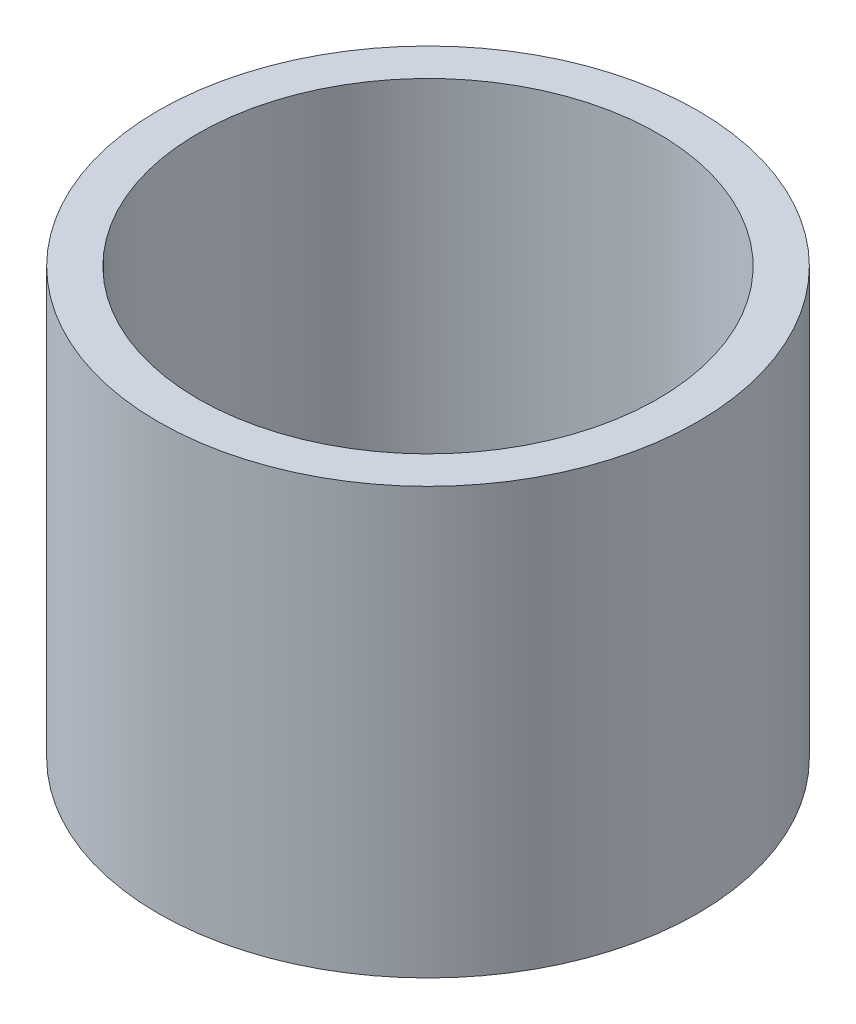
SolidWorks part; units mm, degrees
material "1023 Chapa de acero al carbono (SS)"
ref_plane "Alzado" through (0, 0, 0) normal (0, 0, 1) x (1, 0, 0)
ref_plane "Planta" through (0, 0, 0) normal (0, 1, 0) x (1, 0, 0)
ref_plane "Vista lateral" through (0, 0, 0) normal (1, 0, 0) x (0, 0, -1)
sketch "Sketch1" plane through (0, 0, 0) normal (0, 1, 0) x (1, 0, 0)
  circle A0 centre (0, 0) radius 9.5
  circle A1 centre (0, 0) radius 8.1
  dimension "D1" = 19
  dimension "D2" = 16.2
  dimension "D3" = 1.4
extrude "Extrude1" add sketch "Sketch1" along normal blind 15
